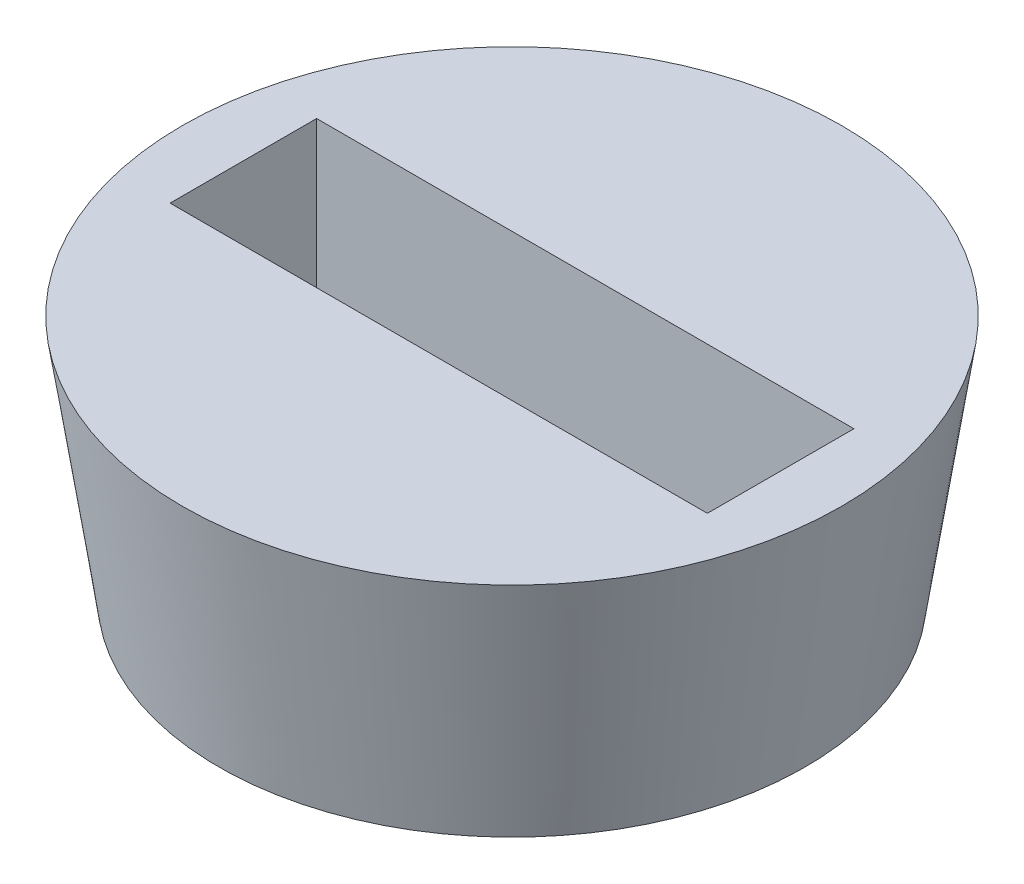
SolidWorks part; units mm, degrees
ref_plane "Front Plane" through (0, 0, 0) normal (0, 0, 1) x (1, 0, 0)
ref_plane "Top Plane" through (0, 0, 0) normal (0, 1, 0) x (1, 0, 0)
ref_plane "Right Plane" through (0, 0, 0) normal (1, 0, 0) x (0, 0, -1)
sketch "Sketch1" plane through (0, 0, 0) normal (0, 0, 1) x (1, 0, 0)
  line L0 (0, 0) -> (0, 5)
  line L1 (0, 5) -> (6.75, 5)
  line L2 (6.75, 5) -> (6, 0)
  line L3 (6, 0) -> (0, 0)
  dimension "D1" = 6
  dimension "D2" = 6.75
  dimension "D3" = 5
revolve "Revolve1" add sketch "Sketch1" angle 360 about L0
sketch "Sketch2" plane through (0, 5, 0) normal (0, 1, 0) x (1, 0, 0)
  line L1 (5.5, 1.5) -> (-5.5, 1.5)
  line L2 (5.5, 1.5) -> (5.5, -1.5)
  line L3 (5.5, -1.5) -> (-5.5, -1.5)
  line L4 (-5.5, 1.5) -> (-5.5, -1.5)
  line L5 (5.5, 1.5) -> (-5.5, -1.5) construction
  line L6 (5.5, -1.5) -> (-5.5, 1.5) construction
  point P0 (0, 0)
  dimension "D1" = 3
  dimension "D2" = 11
extrude "Cut-Extrude1" cut sketch "Sketch2" against normal through all
